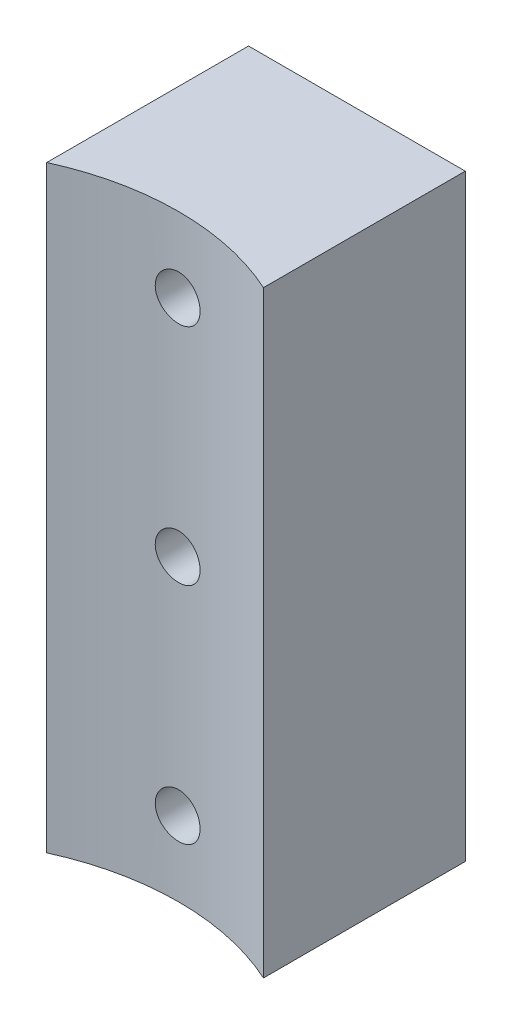
SolidWorks part; units mm, degrees
material "Mahogany"
ref_plane "Front Plane" through (0, 0, 0) normal (0, 0, 1) x (1, 0, 0)
ref_plane "Top Plane" through (0, 0, 0) normal (0, 1, 0) x (1, 0, 0)
ref_plane "Right Plane" through (0, 0, 0) normal (1, 0, 0) x (0, 0, -1)
sketch "Sketch1" plane through (0, 0, 0) normal (0, 1, 0) x (1, 0, 0)
  line L1 (-14.5, 13.5) -> (14.5, 13.5)
  line L2 (-14.5, 13.5) -> (-14.5, -13.5)
  line L4 (14.5, 13.5) -> (14.5, -13.5)
  line L5 (-14.5, 13.5) -> (14.5, -13.5) construction
  line L6 (-14.5, -13.5) -> (14.5, 13.5) construction
  arc A0 (-14.5, -13.5) -> (14.5, -13.5) centre (0, -45.3551) cw
  point P0 (0, 0)
  dimension "D3" = 35
  dimension "D1" = 29
  dimension "D2" = 27
extrude "Boss-Extrude1" add sketch "Sketch1" along normal blind 80
sketch "Sketch2" plane through (0, 0, -13.5) normal (0, 0, -1) x (-1, 0, 0)
  line L0 (-14.5, 0) -> (14.5, 0) construction
  line L1 (-14.5, 80) -> (-14.5, 0) construction
  circle A0 centre (0, 70) radius 3
  circle A1 centre (0, 40) radius 3
  circle A2 centre (0, 10) radius 3
  point P9 (0, 0)
  point P14 (-14.5, 40)
  dimension "D3" = 6
  dimension "D1" = 30
  dimension "D2" = 30
extrude "Cut-Extrude1" cut sketch "Sketch2" against normal through all
